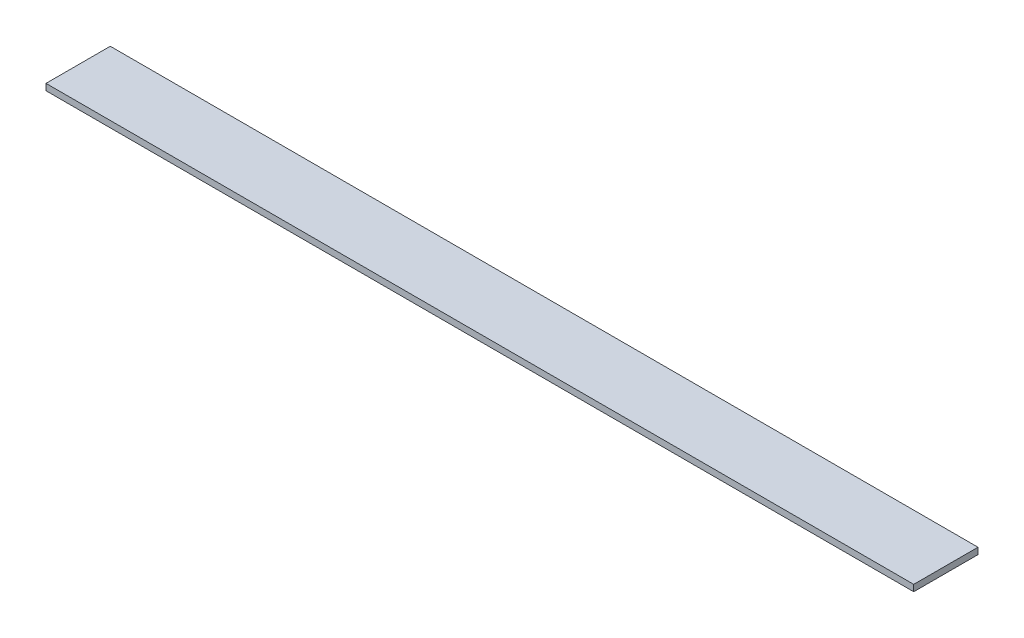
SolidWorks part; units mm, degrees
ref_plane "Face" through (0, 0, 0) normal (0, 0, 1) x (1, 0, 0)
ref_plane "Dessus" through (0, 0, 0) normal (0, 1, 0) x (1, 0, 0)
ref_plane "Droite" through (0, 0, 0) normal (1, 0, 0) x (0, 0, -1)
sketch "Esquisse1" plane through (0, 0, 0) normal (0, 1, 0) x (1, 0, 0)
  line L1 (0, 0) -> (1350, 0)
  line L2 (0, 0) -> (0, 100)
  line L3 (0, 100) -> (1350, 100)
  line L4 (1350, 0) -> (1350, 100)
  dimension "D1" = 1350
  dimension "D2" = 100
extrude "Extrusion1" add sketch "Esquisse1" along normal blind 10
